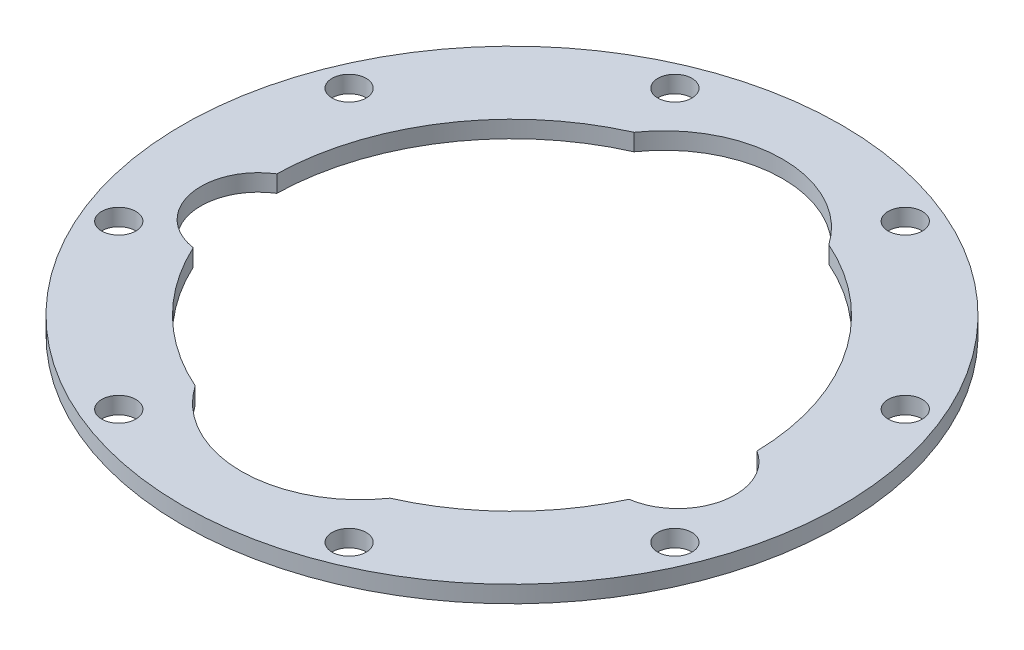
SolidWorks part; units mm, degrees
ref_plane "Front Plane" through (0, 0, 0) normal (0, 0, 1) x (1, 0, 0)
ref_plane "Top Plane" through (0, 0, 0) normal (0, 1, 0) x (1, 0, 0)
ref_plane "Right Plane" through (0, 0, 0) normal (1, 0, 0) x (0, 0, -1)
sketch "Sketch2" plane through (0, 0, 0) normal (0, 1, 0) x (1, 0, 0)
  line L0 (0, 0) -> (0, 48.6568) construction
  line L1 (-34.0588, 82.2253) -> (0, 0) construction
  line L2 (-62, -35.5) -> (-62, 9.5) construction
  line L3 (72.5, -35.5) -> (72.5, 9.5) construction
  line L4 (-62, 9.5) -> (72.5, 9.5) construction
  line L5 (-62, -35.5) -> (72.5, -35.5) construction
  line L6 (0, 0) -> (-34.0588, 0) construction
  circle A0 centre (0, 0) radius 97.45
  arc A4 (-70.9856, 1.4312) -> (-64.4318, -29.8252) centre (-62, -13) ccw
  circle A5 centre (-34.0588, 82.2253) radius 5.05
  circle A6 centre (34.0588, 82.2253) radius 5.05
  circle A7 centre (82.2253, 34.0588) radius 5.05
  circle A8 centre (82.2253, -34.0588) radius 5.05
  circle A9 centre (34.0588, -82.2253) radius 5.05
  circle A10 centre (-34.0588, -82.2253) radius 5.05
  circle A11 centre (-82.2253, -34.0588) radius 5.05
  circle A12 centre (-82.2253, 34.0588) radius 5.05
  circle A13 centre (0, 0) radius 71
  circle A15 centre (0, -45) radius 35
  circle A16 centre (0, 0) radius 77.5 construction
  arc A17 (70.9856, 1.4312) -> (64.4318, -29.8252) centre (62, -13) cw
  circle A18 centre (0, 45) radius 35
  point P31 (-62, -13)
  point P32 (72.5, -13)
  point P41 (0, 0)
  dimension "D2" = 89
  dimension "D3" = 194.9
  dimension "D4" = 10.1
  dimension "D10" = 89
  dimension "D13" = 142
  dimension "D14" = 70
  dimension "D16" = 155
  dimension "D17" = 17
  dimension "D5" = 22.5
  dimension "D6" = 22.5
  dimension "D7" = 62
  dimension "D9" = 89
  dimension "D11" = 45
  dimension "D12" = 45
  dimension "D15" = 45
  dimension "D18" = 9.5
  dimension "D8" = 8
extrude "Boss-Extrude1" add sketch "Sketch2" along normal blind 5 contours A0 A12 A11 A10 A9 A8 A7 A6 A5 A13 A18 A17 A15 A4
